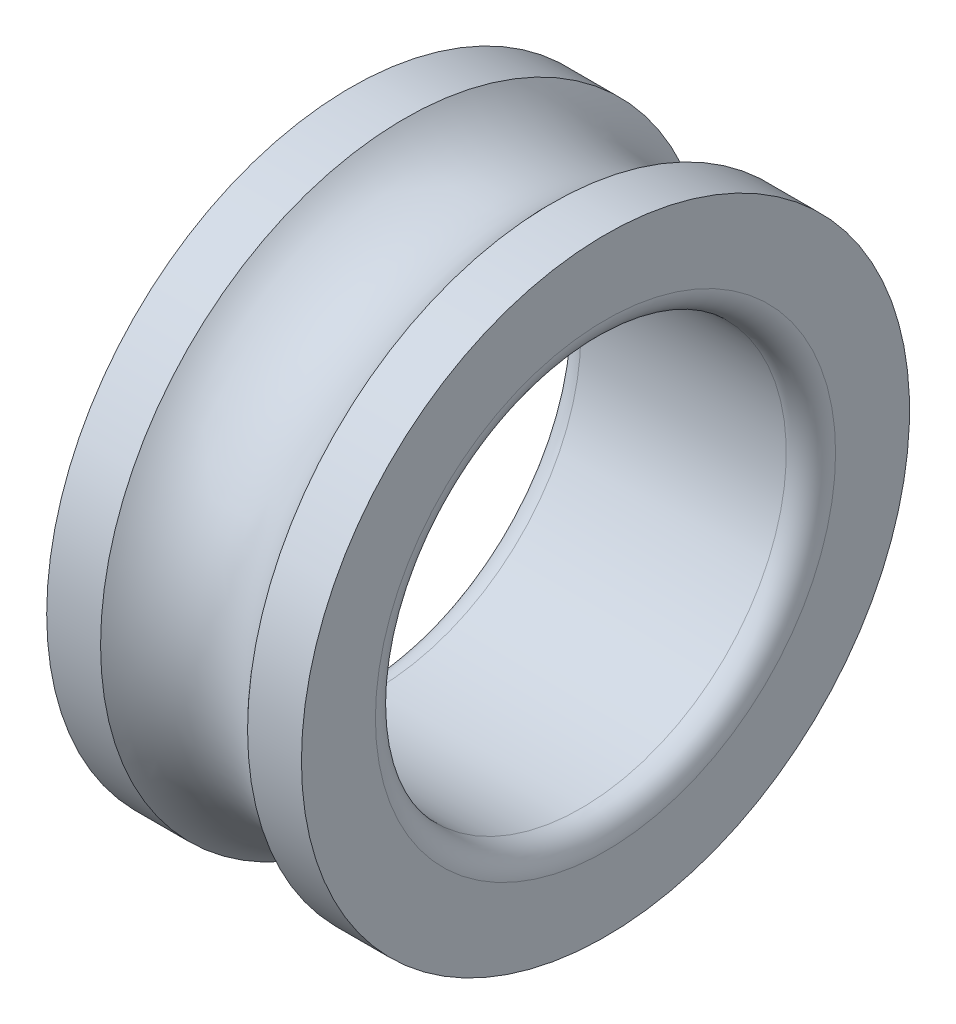
SolidWorks part; units mm, degrees
ref_plane "Front Plane" through (0, 0, 0) normal (0, 0, 1) x (1, 0, 0)
ref_plane "Top Plane" through (0, 0, 0) normal (0, 1, 0) x (1, 0, 0)
ref_plane "Right Plane" through (0, 0, 0) normal (1, 0, 0) x (0, 0, -1)
sketch "Sketch1" plane through (0, 0, 0) normal (0, 0, 1) x (1, 0, 0)
  line L0 (-22.6164, 0) -> (28.9528, 0) construction
  line L1 (0, 45.2445) -> (0, 37) construction
  line L2 (-15.5, 25) -> (15.5, 25)
  line L3 (-15.5, 25) -> (-15.5, 37)
  line L4 (-15.5, 37) -> (-8.9443, 37)
  line L5 (15.5, 25) -> (15.5, 37)
  line L6 (-15.5, 25) -> (15.5, 37) construction
  line L7 (-15.5, 37) -> (15.5, 25) construction
  line L8 (8.9443, 37) -> (15.5, 37)
  line L9 (0, 33) -> (0, -4.3255) construction
  arc A0 (-8.9443, 37) -> (8.9443, 37) centre (0, 45) ccw
  point P3 (0, 31)
  point P13 (0, 0)
  dimension "D5" = 12
  dimension "D1" = 31
  dimension "D2" = 25
  dimension "D3" = 37
  dimension "D4" = 8
revolve "Revolve1" add sketch "Sketch1" angle 360 about L0
fillet "Fillet1" radius 3 2 edges at (-15.5, 0, 25) (15.5, 0, 25)
